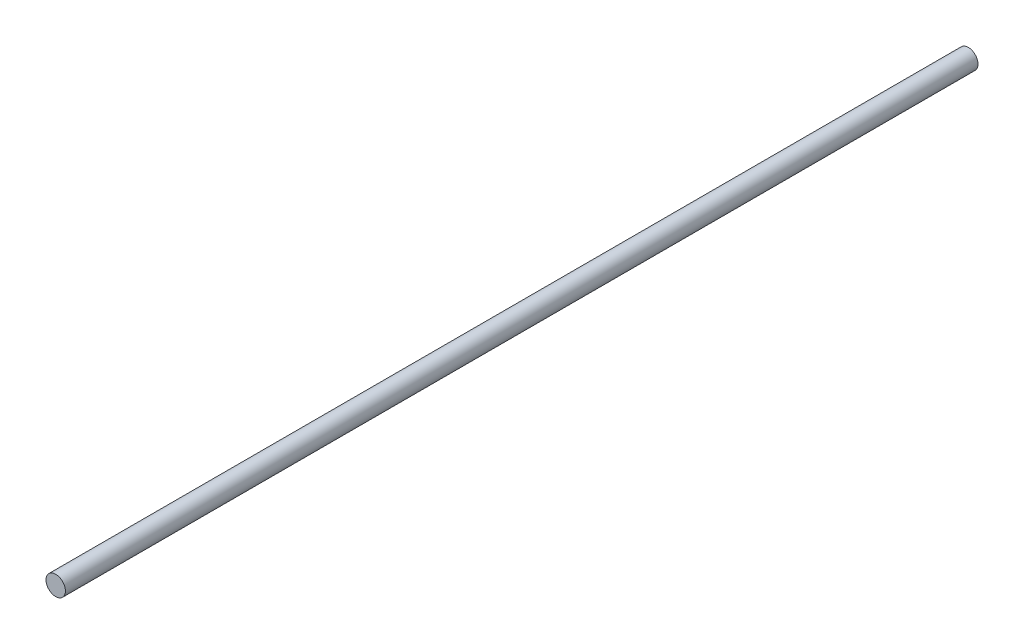
SolidWorks part; units mm, degrees
material "Plain Carbon Steel"
ref_plane "Front Plane" through (0, 0, 0) normal (0, 0, 1) x (1, 0, 0)
ref_plane "Top Plane" through (0, 0, 0) normal (0, 1, 0) x (1, 0, 0)
ref_plane "Right Plane" through (0, 0, 0) normal (1, 0, 0) x (0, 0, -1)
sketch "Sketch1" plane through (0, 0, 0) normal (0, 0, 1) x (1, 0, 0)
  line L5 (-1.7678, 1.7678) -> (1.7678, -1.7678) construction
  line L6 (-1.7678, -1.7678) -> (1.7678, 1.7678) construction
  circle A0 centre (0, 0) radius 2.5
  point P0 (0, 0)
  dimension "D3" = 5
extrude "Boss-Extrude1" add sketch "Sketch1" along normal mid plane 235
sketch "Sketch2" plane through (0, 0, 117.5) normal (0, 0, 1) x (1, 0, 0)
  circle A0 centre (0, 0) radius 4.7826
